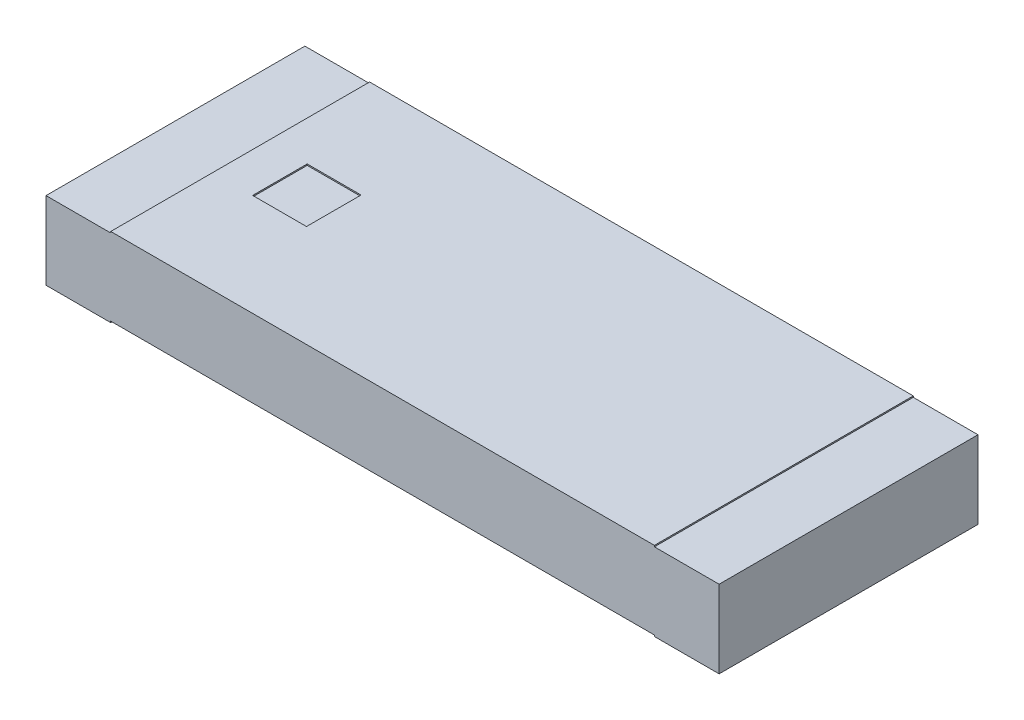
SolidWorks part; units mm, degrees
ref_plane "Спереди" through (0, 0, 0) normal (0, 0, 1) x (1, 0, 0)
ref_plane "Сверху" through (0, 0, 0) normal (0, 1, 0) x (1, 0, 0)
ref_plane "Справа" through (0, 0, 0) normal (1, 0, 0) x (0, 0, -1)
sketch "Эскиз1" plane through (0, 0, 0) normal (0, 1, 0) x (1, 0, 0)
  line L1 (-2.6, 1) -> (2.6, 1)
  line L2 (-2.6, 1) -> (-2.6, -1)
  line L3 (-2.6, -1) -> (2.6, -1)
  line L4 (2.6, 1) -> (2.6, -1)
  line L5 (-2.6, 1) -> (2.6, -1) construction
  line L6 (-2.6, -1) -> (2.6, 1) construction
  point P0 (0, 0)
  dimension "D1" = 5.2
  dimension "D2" = 2
extrude "Бобышка-Вытянуть1" add sketch "Эскиз1" along normal blind 0.6
sketch "Эскиз2" plane through (0, 0.6, 0) normal (0, 1, 0) x (1, 0, 0)
  line L1 (-2.1, 1) -> (2.1, 1)
  line L2 (-2.1, 1) -> (-2.1, -1)
  line L3 (-2.1, -1) -> (2.1, -1)
  line L4 (2.1, 1) -> (2.1, -1)
  line L5 (-2.1, 1) -> (2.1, -1) construction
  line L6 (-2.1, -1) -> (2.1, 1) construction
  point P0 (0, 0)
  dimension "D1" = 2
  dimension "D2" = 4.2
extrude "Бобышка-Вытянуть2" add sketch "Эскиз2" along normal blind 0.01 contours L2 L1 L4 L3
sketch "Эскиз3" plane through (0, 0.61, 0) normal (0, 1, 0) x (1, 0, 0)
  line L1 (-1.7929, 0.2108) -> (-1.3767, 0.2108)
  line L2 (-1.7929, 0.2108) -> (-1.7929, -0.2108)
  line L3 (-1.7929, -0.2108) -> (-1.3767, -0.2108)
  line L4 (-1.3767, 0.2108) -> (-1.3767, -0.2108)
  line L5 (-1.7929, 0.2108) -> (-1.3767, -0.2108) construction
  line L6 (-1.7929, -0.2108) -> (-1.3767, 0.2108) construction
  point P0 (-1.5848, 0)
extrude "Вырез-Вытянуть1" cut sketch "Эскиз3" against normal blind 0.01
sketch "Эскиз4" plane through (0, 0, 0) normal (0, -1, 0) x (1, 0, 0)
  line L1 (-2.1, 1) -> (2.1, 1)
  line L2 (-2.1, 1) -> (-2.1, -1)
  line L3 (-2.1, -1) -> (2.1, -1)
  line L4 (2.1, 1) -> (2.1, -1)
  line L5 (-2.1, 1) -> (2.1, -1) construction
  line L6 (-2.1, -1) -> (2.1, 1) construction
  point P0 (0, 0)
  dimension "D1" = 2
  dimension "D2" = 4.2
extrude "Вырез-Вытянуть2" cut sketch "Эскиз4" against normal blind 0.01
